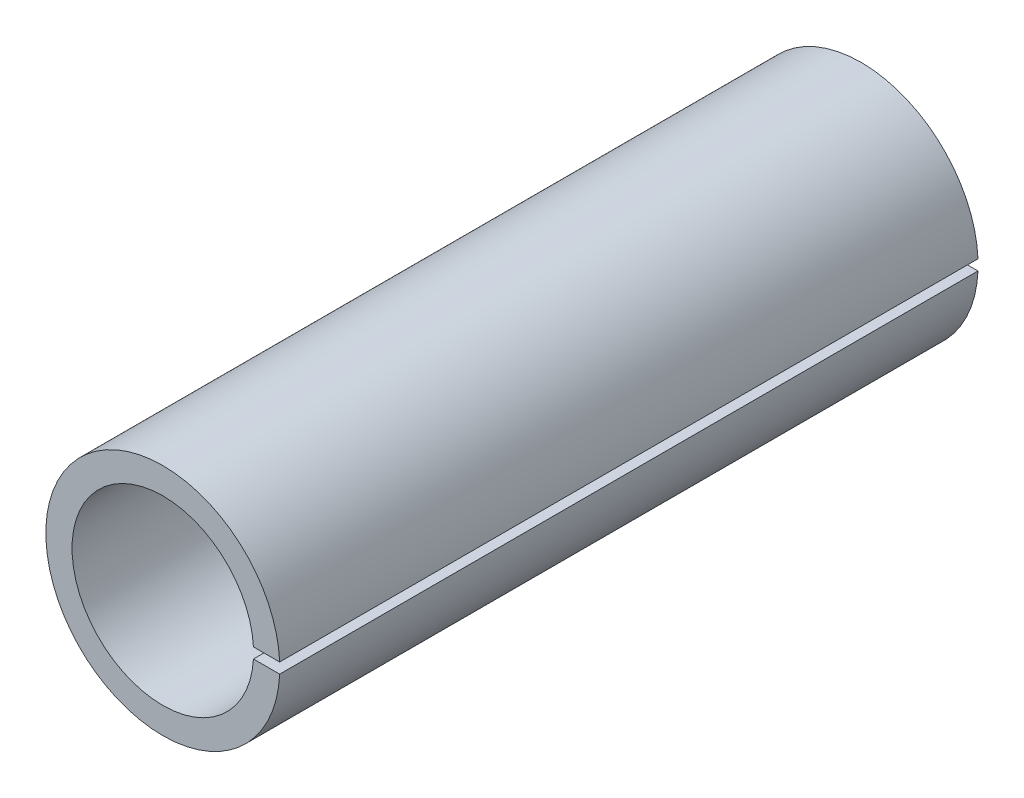
SolidWorks part; units mm, degrees
material "Alloy Steel"
ref_plane "Front Plane" through (0, 0, 0) normal (0, 0, 1) x (1, 0, 0)
ref_plane "Top Plane" through (0, 0, 0) normal (0, 1, 0) x (1, 0, 0)
ref_plane "Right Plane" through (0, 0, 0) normal (1, 0, 0) x (0, 0, -1)
sketch "Sketch1" plane through (0, 0, 0) normal (0, 0, 1) x (1, 0, 0)
  line L0 (0, 3.302) -> (0, 4.2545) construction
  line L1 (0, -3.302) -> (0, -4.2545) construction
  line L2 (3.2965, 0.1905) -> (4.2502, 0.1905)
  line L3 (3.2965, -0.1905) -> (4.2502, -0.1905)
  arc A0 (4.2502, 0.1905) -> (4.2502, -0.1905) centre (0, 0) ccw
  arc A1 (3.2965, 0.1905) -> (3.2965, -0.1905) centre (0, 0) ccw
  dimension "D1" = 0.381
  dimension "OD" = 8.509
  dimension "ID" = 6.604
sketch "Sketch2" plane through (0, 0, 0) normal (1, 0, 0) x (0, 0, -1)
  line L0 (-12.7, 3.302) -> (12.7, 3.302) construction
  line L1 (-12.7, -3.302) -> (12.7, -3.302) construction
  line L2 (-12.7, -4.2545) -> (12.7, -4.2545) construction
  line L3 (-12.7, 4.2545) -> (12.7, 4.2545) construction
  dimension "Length" = 25.4
extrude "Extrude1" add sketch "Sketch1" along normal up to vertex (12.7 mm away) and the other way up to vertex (12.7 mm away) up to point (0, 3.302, 12.7) other way up to point (0, 3.302, -12.7)
sketch "Sketch3" plane through (0, 0, 12.7) normal (0, 0, 1) x (1, 0, 0)
  circle A0 centre (0, 0) radius 3.302 construction
  circle A3 centre (0, 0) radius 3.302
  point P3 (-3.302, 0)
